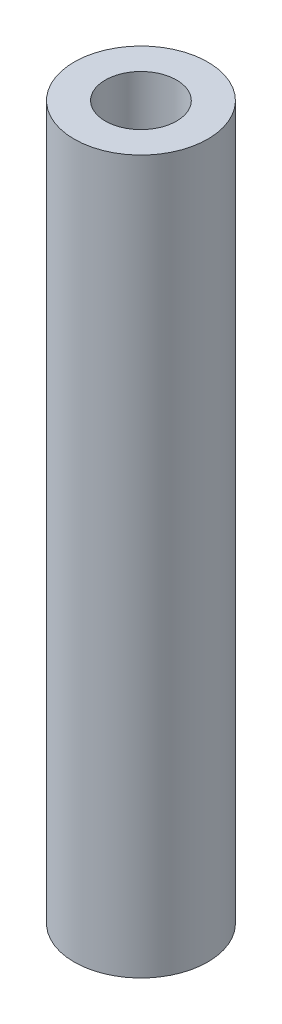
SolidWorks part; units mm, degrees
ref_plane "Front Plane" through (0, 0, 0) normal (0, 0, 1) x (1, 0, 0)
ref_plane "Top Plane" through (0, 0, 0) normal (0, 1, 0) x (1, 0, 0)
ref_plane "Right Plane" through (0, 0, 0) normal (1, 0, 0) x (0, 0, -1)
sketch "Sketch2" plane through (0, 0, 0) normal (0, 1, 0) x (1, 0, 0)
  circle A0 centre (0, 0) radius 9.525
extrude "Boss-Extrude1" add sketch "Sketch2" along normal blind 101.6
sketch "Sketch3" plane through (0, 101.6, 0) normal (0, 1, 0) x (1, 0, 0)
  circle A0 centre (0, 0) radius 5.08
extrude "Cut-Extrude1" cut sketch "Sketch3" against normal through all
